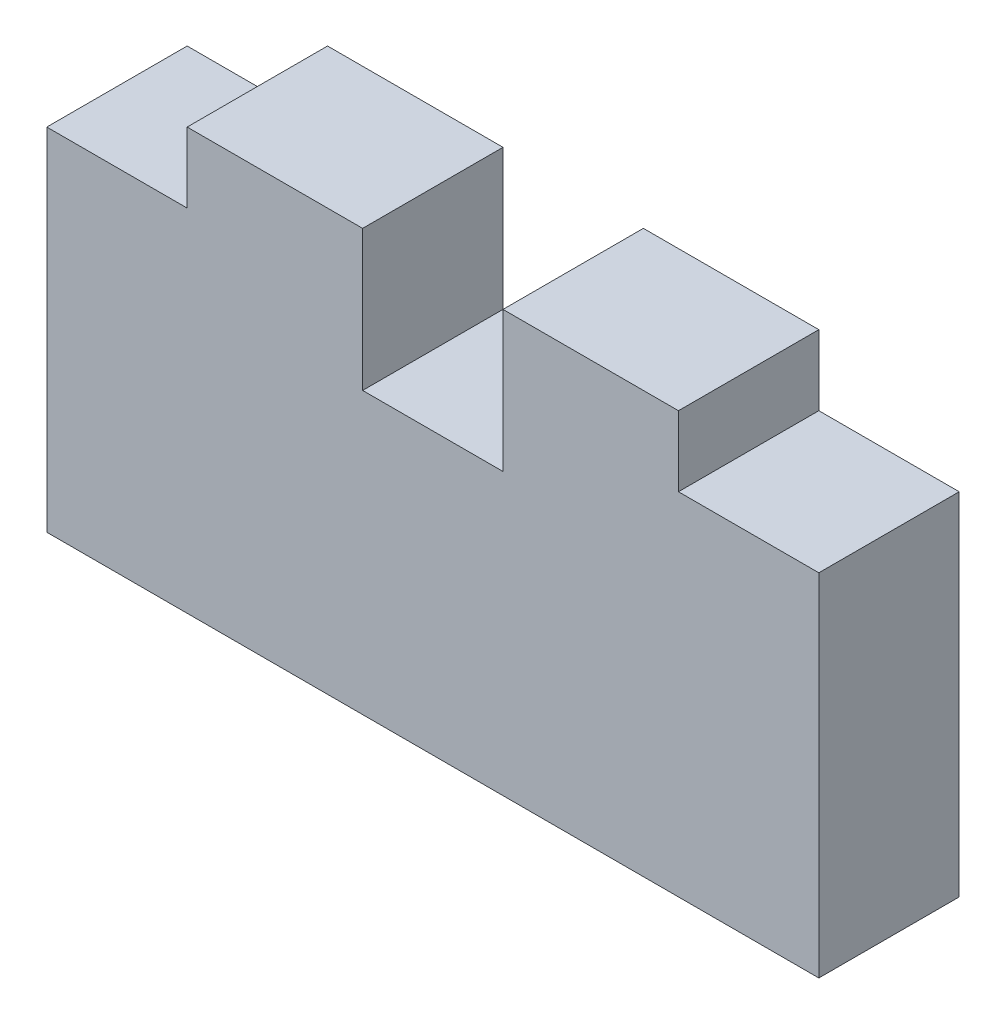
SolidWorks part; units mm, degrees
ref_plane "Front Plane" through (0, 0, 0) normal (0, 0, 1) x (1, 0, 0)
ref_plane "Top Plane" through (0, 0, 0) normal (0, 1, 0) x (1, 0, 0)
ref_plane "Right Plane" through (0, 0, 0) normal (1, 0, 0) x (0, 0, -1)
sketch "Sketch1" plane through (0, 0, 0) normal (0, 0, 1) x (1, 0, 0)
  line L0 (0, 0) -> (17.4625, 0)
  line L1 (17.4625, 0) -> (17.4625, 7.9375)
  line L2 (17.4625, 7.9375) -> (14.2875, 7.9375)
  line L3 (14.2875, 7.9375) -> (14.2875, 9.525)
  line L4 (14.2875, 9.525) -> (10.3187, 9.525)
  line L5 (10.3187, 9.525) -> (10.3187, 6.35)
  line L6 (10.3187, 6.35) -> (7.1437, 6.35)
  line L7 (7.1437, 6.35) -> (7.1437, 9.525)
  line L8 (7.1437, 9.525) -> (3.175, 9.525)
  line L9 (3.175, 9.525) -> (3.175, 7.9375)
  line L10 (3.175, 7.9375) -> (0, 7.9375)
  line L11 (0, 7.9375) -> (0, 0)
  point P12 (8.7312, 6.35)
  point P14 (8.7312, 0)
  dimension "D1" = 3.175
  dimension "D2" = 9.525
  dimension "D3" = 7.9375
  dimension "D4" = 3.175
  dimension "D5" = 17.4625
  dimension "D6" = 11.1125
  dimension "D7" = 3.175
extrude "Boss-Extrude2" add sketch "Sketch1" along normal blind 3.175 contours L8 L9 L10 L11 L0 L1 L2 L3 L4 L5 L6 L7
